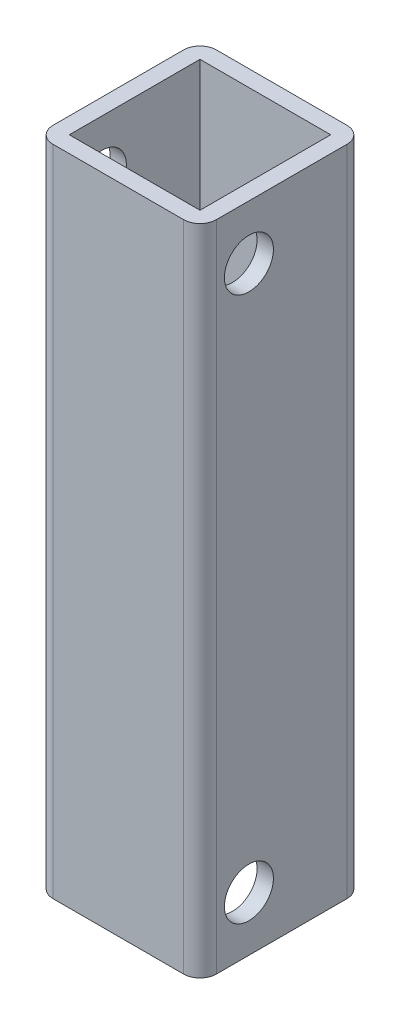
SolidWorks part; units mm, degrees
ref_plane "Alzado" through (0, 0, 0) normal (0, 0, 1) x (1, 0, 0)
ref_plane "Planta" through (0, 0, 0) normal (0, 1, 0) x (1, 0, 0)
ref_plane "Vista lateral" through (0, 0, 0) normal (1, 0, 0) x (0, 0, -1)
ref_plane "Plano1" through (0, 0, -20.1201) normal (0, 0, 1) x (1, 0, 0)
sketch "Croquis1" plane through (0, 0, -20.1201) normal (0, 0, 1) x (1, 0, 0)
  line L0 (-15, 387.9345) -> (15, 387.9345)
  line L1 (15, 387.9345) -> (15, 507.9)
  line L2 (15, 507.9) -> (-15, 507.9)
  line L3 (-15, 507.9) -> (-15, 387.9345)
extrude "Saliente-Extruir1" add sketch "Croquis1" against normal blind 30
sketch "Croquis2" plane through (0, 507.9, 0) normal (0, 1, 0) x (-1, 0, 0)
  line L0 (12, -23.1201) -> (-12, -23.1201)
  line L1 (-12, -23.1201) -> (-12, -47.1201)
  line L2 (-12, -47.1201) -> (12, -47.1201)
  line L3 (12, -47.1201) -> (12, -23.1201)
extrude "Cortar-Extruir1" cut sketch "Croquis2" against normal through all
hole_wizard "Diámetro de taladro Ø9.0 (9)1" positions "Croquis4" profile "Croquis3" hole size "Ø9.0" standard "Ansi Metric"
sketch "Croquis4" plane through (-12, 0, 0) normal (1, 0, 0) x (0, 0, -1)
  point P0 (29.1, 397.9345)
  point P1 (29.1, 497.9345)
sketch "Croquis3" plane through (-12, 397.9345, -29.1) normal (0, 1, 0) x (0, 0, -1)
  line L0 (0, 0) -> (0, 3)
  line L1 (0, 3) -> (4.5, 3)
  line L2 (4.5, 3) -> (4.5, 0)
  line L5 (4.5, 0) -> (0, 0)
  line L11 (0, -6.35) -> (0, 107.95) construction
  dimension "Diámetro de taladro hasta el siguiente" = 9
  dimension "Profundidad de taladro hasta el siguiente" = 3
hole_wizard "Diámetro de taladro Ø9.0 (9)2" positions "Croquis6" profile "Croquis5" hole size "Ø9.0" standard "Ansi Metric"
sketch "Croquis6" plane through (15, 0, 0) normal (1, 0, 0) x (0, 0, -1)
  point P0 (29.1, 497.9345)
  point P1 (29.1, 397.9345)
sketch "Croquis5" plane through (15, 497.9345, -29.1) normal (0, 1, 0) x (0, 0, -1)
  line L0 (0, 0) -> (0, 30)
  line L1 (0, 30) -> (4.5, 30)
  line L2 (4.5, 30) -> (4.5, 0)
  line L5 (4.5, 0) -> (0, 0)
  line L11 (0, -6.35) -> (0, 107.95) construction
  dimension "Diámetro de taladro hasta el siguiente" = 9
  dimension "Profundidad de taladro hasta el siguiente" = 30
fillet "Redondeo1" radius 3 4 edges at (15, 447.9173, -50.1201) (-15, 447.9173, -50.1201) (15, 447.9173, -20.1201) (-15, 447.9173, -20.1201)
